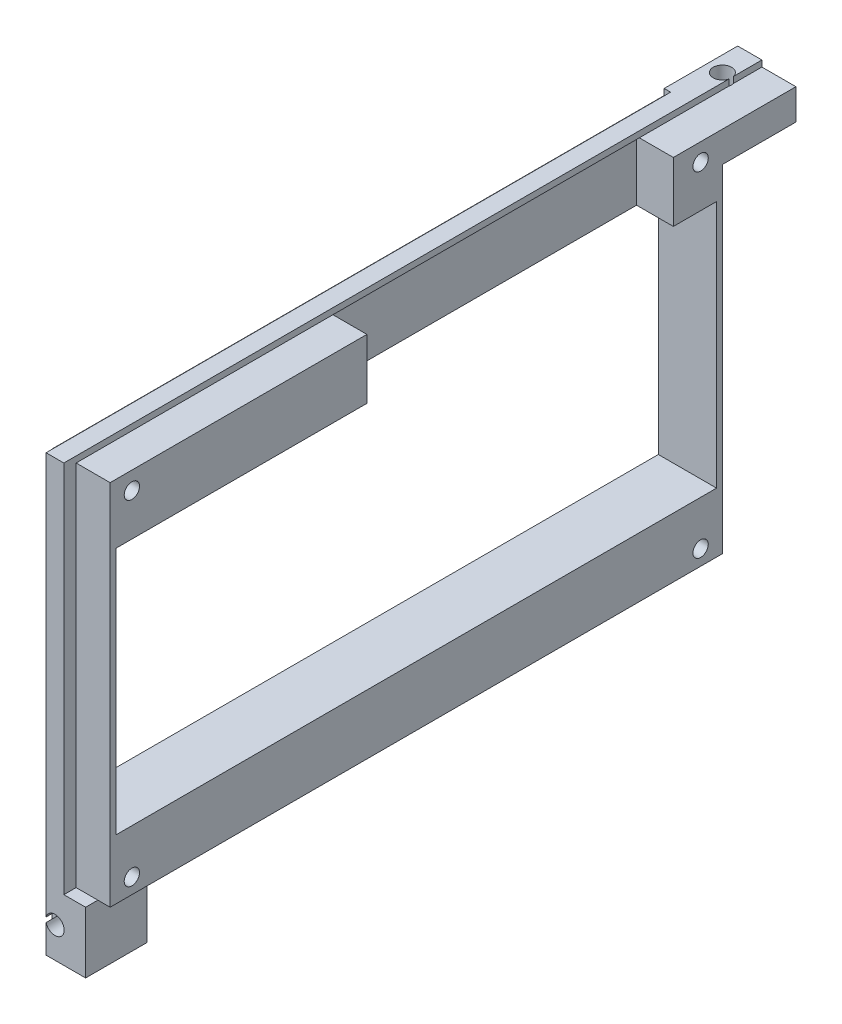
SolidWorks part; units mm, degrees
ref_plane "Front Plane" through (0, 0, 0) normal (0, 0, 1) x (1, 0, 0)
ref_plane "Top Plane" through (0, 0, 0) normal (0, 1, 0) x (1, 0, 0)
ref_plane "Right Plane" through (0, 0, 0) normal (1, 0, 0) x (0, 0, -1)
sketch "Esquisse1" plane through (0, 0, 0) normal (0, 0, 1) x (1, 0, 0)
  line L0 (0, 60) -> (12, 60)
  line L1 (12, 60) -> (12, 0)
  line L2 (12, 0) -> (0, 0)
  line L7 (0, 0) -> (0, 60)
  dimension "D1" = 12
  dimension "D2" = 60
  dimension "D6" = 12
extrude "Main" add sketch "Esquisse1" along normal mid plane 99.9
sketch "Esquisse2" plane through (12, 0, 0) normal (1, 0, 0) x (0, 0, -1)
  line L1 (-46.4, 2.5) -> (46.4, 2.5) construction
  line L2 (-49.95, 0) -> (49.95, 0) construction
  line L3 (-49.95, 60) -> (49.95, 60) construction
  circle A0 centre (46.4, 2.5) radius 1.25
  circle A1 centre (-46.4, 2.5) radius 1.25
  circle A2 centre (46.4, 57.1) radius 1.25
  circle A3 centre (-46.4, 57.1) radius 1.25
  point P8 (0, 60)
  point P9 (0, 2.5)
  dimension "D1" = 92.8
  dimension "D4" = 54.6
  dimension "D3" = 2.5
  dimension "D2" = 2.5
extrude "HolesFixForLCD" cut sketch "Esquisse2" against normal through all
sketch "Sketch1" plane through (12, 0, 0) normal (1, 0, 0) x (0, 0, -1)
  line L0 (-49.95, 60) -> (49.95, 60) construction
  line L1 (49, 9.75) -> (-49, 9.75)
  line L2 (49, 9.75) -> (49, 50.25)
  line L3 (49, 50.25) -> (-49, 50.25)
  line L4 (-49, 9.75) -> (-49, 50.25)
  line L7 (49.95, 0) -> (49.95, 60) construction
  point P4 (49, 30)
  point P5 (49.95, 30)
  point P6 (0, 60)
  point P12 (0, 50.25)
  dimension "D1" = 98
  dimension "D4" = 40.5
extrude "LCDWindowHole" cut sketch "Sketch1" against normal through all
sketch "Sketch6" plane through (0, 60, 0) normal (0, 1, 0) x (1, 0, 0)
  line L0 (12, 49.95) -> (0, 49.95) construction
  line L1 (3.55, 51.95) -> (6.45, 51.95)
  line L2 (3.55, 51.95) -> (3.55, 49.95)
  line L3 (3.55, 49.95) -> (6.45, 49.95)
  line L4 (6.45, 51.95) -> (6.45, 49.95)
  line L6 (0, -49.95) -> (0, 49.95) construction
  line L7 (12, -49.95) -> (0, -49.95) construction
  line L8 (3.55, -49.95) -> (6.45, -49.95)
  line L9 (3.55, -49.95) -> (3.55, -51.95)
  line L10 (3.55, -51.95) -> (6.45, -51.95)
  line L11 (6.45, -49.95) -> (6.45, -51.95)
  dimension "D1" = 2
  dimension "D2" = 3.55
  dimension "D3" = 2.9
extrude "MakerBeamRail" add sketch "Sketch6" against normal up to surface (60 mm away) up to face at (6, 0, 0)
sketch "Sketch7" plane through (12, 0, 0) normal (1, 0, 0) x (0, 0, -1)
  line L0 (-49.95, 60) -> (49.95, 60) construction
  line L1 (-8.05, 60) -> (41.95, 60)
  line L2 (-8.05, 60) -> (-8.05, 50.25)
  line L3 (-8.05, 50.25) -> (41.95, 50.25)
  line L4 (41.95, 60) -> (41.95, 50.25)
  line L5 (49.95, 0) -> (49.95, 60) construction
  line L6 (49, 50.25) -> (-49, 50.25) construction
  dimension "D1" = 8
  dimension "D2" = 50
extrude "LCDPinsHoles" cut sketch "Sketch7" against normal blind 6
sketch "Sketch8" plane through (0, 0, 0) normal (-1, 0, 0) x (0, 0, 1)
  line L0 (49, 9.75) -> (-49, 9.75) construction
  line L1 (-49, 50.25) -> (-41, 50.25)
  line L2 (-49, 50.25) -> (-49, 9.75)
  line L3 (-49, 9.75) -> (-41, 9.75)
  line L4 (-41, 50.25) -> (-41, 9.75)
  line L6 (49, 50.25) -> (41, 50.25)
  line L7 (49, 50.25) -> (49, 9.75)
  line L8 (49, 9.75) -> (41, 9.75)
  line L9 (41, 50.25) -> (41, 9.75)
  dimension "D1" = 8
extrude "Reinforcement" add sketch "Sketch8" against normal blind 2.5 separate body
sketch "Sketch12" plane through (0, 0, 51.95) normal (0, 0, 1) x (1, 0, 0)
  line L0 (0, 60) -> (0, 0) construction
  line L1 (0, 0) -> (2.5, 0)
  line L2 (0, 0) -> (0, 69)
  line L3 (0, 69) -> (2.5, 69)
  line L4 (2.5, 0) -> (2.5, 69)
  point P6 (0, 0)
  point P8 (0, 60)
  point P9 (0, 67)
  dimension "D1" = 2.5
extrude "WindowPlasticHole" cut sketch "Sketch12" against normal through all
sketch "Sketch13" plane through (0, 0, 51.95) normal (0, 0, 1) x (1, 0, 0)
  line L1 (3.55, 60) -> (6.45, 60)
  line L2 (3.55, 60) -> (3.55, 61)
  line L3 (3.55, 61) -> (6.45, 61)
  line L4 (6.45, 60) -> (6.45, 61)
  point P5 (6.45, 60)
  dimension "D1" = 1
extrude "MakerBeamRailUp" add sketch "Sketch13" against normal up to surface (103.9 mm away) up to face at (5, 30, -51.95)
sketch "Sketch14" plane through (0, 0, -49.95) normal (0, 0, -1) x (-1, 0, 0)
  line L0 (-12, 60) -> (-6.45, 60)
  line L2 (-12, 60) -> (-6.45, 60) construction
  line L3 (-6.45, 60) -> (-6.45, 61)
  line L4 (-6.45, 61) -> (-2.5, 61)
  line L5 (-2.5, 61) -> (-2.5, 55)
  line L7 (-2.5, 55) -> (-12, 55)
  line L8 (-12, 0) -> (-12, 60) construction
  line L9 (-12, 55) -> (-12, 60)
  line L10 (-2.5, 60) -> (-2.5, 0) construction
  point P3 (-3.55, 55)
  point P4 (-2.5, 55)
  point P14 (0, 0)
  point P18 (-2.5, 61)
  dimension "D1" = 5
extrude "Boss-Extrude2" add sketch "Sketch14" along normal blind 12
sketch "Sketch15" plane through (0, 55, 0) normal (0, -1, 0) x (1, 0, 0)
  line L1 (3.55, -51.95) -> (6.45, -51.95) construction
  line L2 (12, -61.95) -> (2.5, -61.95) construction
  circle A0 centre (5, -56.95) radius 1.5
  point P2 (0, 0)
  point P4 (5, -51.95)
  point P10 (-6.5521, -47.5253)
  dimension "D1" = 3
  dimension "D2" = 5
extrude "Cut-Extrude4" cut sketch "Sketch15" against normal through all
sketch "Sketch16" plane through (0, 0, 0) normal (0, -1, 0) x (-1, 0, 0)
  line L0 (-2.5, -49.95) -> (-3.55, -49.95)
  line L2 (-3.55, -49.95) -> (-3.55, -51.95)
  line L3 (-3.55, -51.95) -> (-10, -51.95)
  line L4 (-10, -51.95) -> (-10, -41.95)
  line L5 (-10, -41.95) -> (-2.5, -41.95)
  line L6 (-2.5, 49.95) -> (-2.5, -49.95) construction
  line L19 (-3.55, -49.95) -> (-2.5, -49.95)
  line L20 (-2.5, -49.95) -> (-2.5, 49.95)
  line L21 (-2.5, 49.95) -> (-3.55, 49.95)
  line L22 (-3.55, 49.95) -> (-3.55, 51.95)
  line L23 (-3.55, 51.95) -> (-6.45, 51.95)
  line L24 (-6.45, 51.95) -> (-6.45, 49.95)
  line L25 (-6.45, 49.95) -> (-12, 49.95)
  line L26 (-12, 49.95) -> (-12, -49.95)
  line L27 (-12, -49.95) -> (-6.45, -49.95)
  line L28 (-6.45, -49.95) -> (-6.45, -51.95)
  line L29 (-6.45, -51.95) -> (-3.55, -51.95)
  line L30 (-3.55, -51.95) -> (-3.55, -49.95)
  line L32 (-2.5, -49.95) -> (-2.5, -41.95)
  point P2 (-2.5, -49.95)
  point P12 (0, 0)
  point P13 (-3.025, -49.95)
  dimension "D1" = 7.5
  dimension "D2" = 10
  dimension "D3" = 0
extrude "Boss-Extrude3" add sketch "Sketch16" along normal blind 10
sketch "Sketch17" plane through (0, 0, 51.95) normal (0, 0, 1) x (1, 0, 0)
  line L0 (10, -10) -> (3.55, -10) construction
  line L2 (3.55, 0) -> (6.45, 0) construction
  circle A0 centre (5, -5) radius 1.5
  point P4 (6.775, -10)
  point P5 (5, 0)
  point P6 (0, 0)
  dimension "D1" = 3
  dimension "D2" = 5
extrude "Cut-Extrude5" cut sketch "Sketch17" against normal through all
